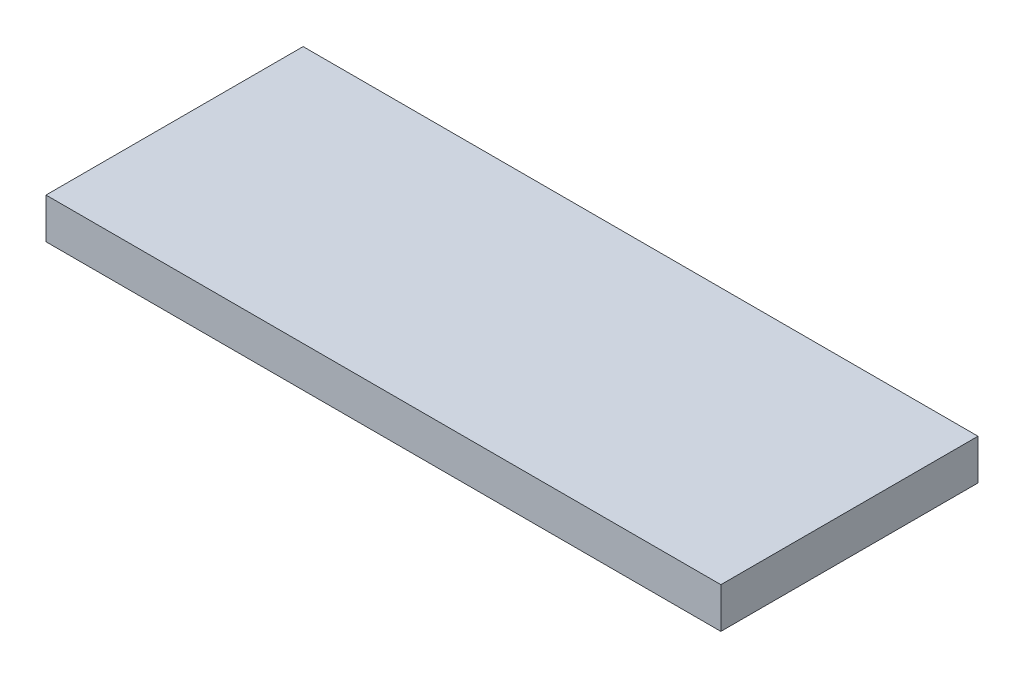
SolidWorks part; units mm, degrees
material "Melamine resin"
ref_plane "Front Plane" through (0, 0, 0) normal (0, 0, 1) x (1, 0, 0)
ref_plane "Top Plane" through (0, 0, 0) normal (0, 1, 0) x (1, 0, 0)
ref_plane "Right Plane" through (0, 0, 0) normal (1, 0, 0) x (0, 0, -1)
sketch "Sketch1" plane through (0, 0, 0) normal (0, 1, 0) x (1, 0, 0)
  line L1 (-25, -9.525) -> (25, -9.525)
  line L2 (-25, -9.525) -> (-25, 9.525)
  line L3 (-25, 9.525) -> (25, 9.525)
  line L4 (25, -9.525) -> (25, 9.525)
  line L5 (-25, -9.525) -> (25, 9.525) construction
  line L6 (-25, 9.525) -> (25, -9.525) construction
  point P0 (0, 0)
  dimension "D1" = 50
  dimension "D2" = 19.05
extrude "Boss-Extrude1" add sketch "Sketch1" along normal blind 3
